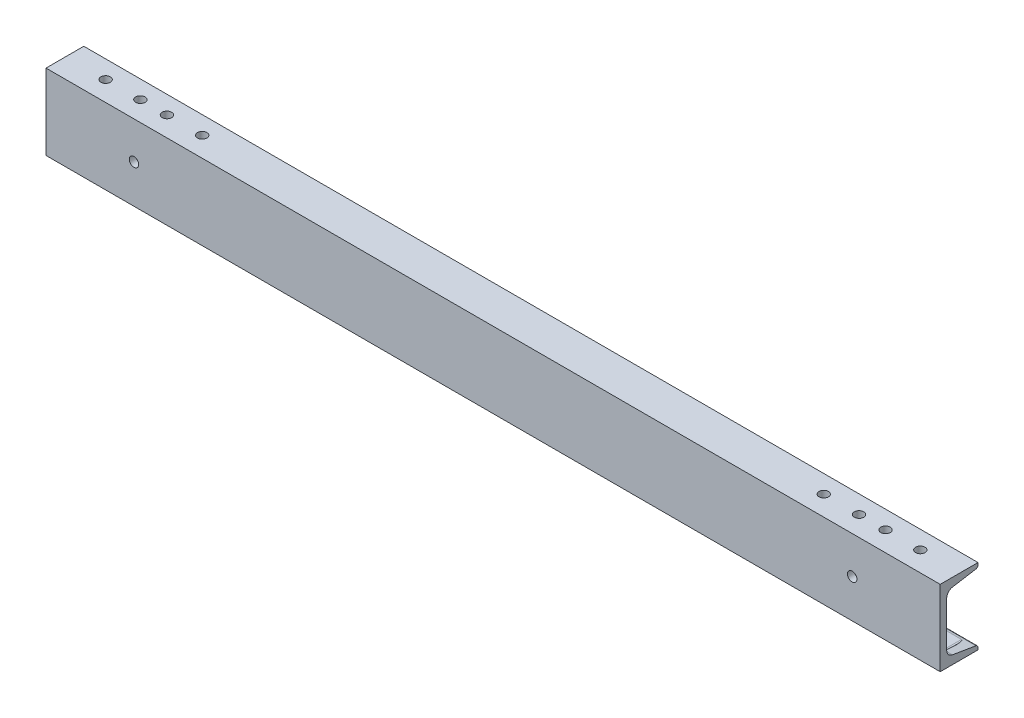
SolidWorks part; units mm, degrees
material "Plain Carbon Steel"
ref_plane "Front Plane" through (0, 0, 0) normal (0, 0, 1) x (1, 0, 0)
ref_plane "Top Plane" through (0, 0, 0) normal (0, 1, 0) x (1, 0, 0)
ref_plane "Right Plane" through (0, 0, 0) normal (1, 0, 0) x (0, 0, -1)
sketch "Sketch1" plane through (0, 0, 0) normal (0, 1, 0) x (1, 0, 0)
  line L0 (-450, 0) -> (450, 0)
  dimension "D1" = 900
other "Structural Member1"
ref_plane "Plane1" through (-450, 0, 0) normal (1, 0, 0) x (0, 0, -1)
sketch "Sketch11" plane through (-450, 0, 0) normal (1, 0, 0) x (0, 0, -1)
  line L0 (0, -38.1) -> (0, 38.1)
  line L1 (0, 38.1) -> (38.0492, 38.1)
  line L2 (0, -38.1) -> (38.0492, -38.1)
  line L5 (31.75, -31.1658) -> (6.35, -31.1658) construction
  line L6 (0, 0) -> (6.5532, 0) construction
  line L12 (6.5532, 22.7314) -> (6.5532, -22.7314)
  line L15 (38.0492, 38.1) -> (38.0492, 35.9423)
  line L16 (38.0492, -38.1) -> (38.0492, -35.9423)
  line L17 (12.2837, 29.4961) -> (35.9268, 33.4369)
  line L18 (12.2837, -29.4961) -> (35.9268, -33.4369)
  arc A9 (6.5532, -22.7314) -> (12.2837, -29.4961) centre (13.4112, -22.7314) ccw
  arc A10 (6.5532, 22.7314) -> (12.2837, 29.4961) centre (13.4112, 22.7314) cw
  arc A11 (38.0492, 35.9423) -> (35.9268, 33.4369) centre (35.5092, 35.9423) cw
  arc A12 (38.0492, -35.9423) -> (35.9268, -33.4369) centre (35.5092, -35.9423) ccw
  point P4 (38.0492, 33.7907)
  point P5 (38.0492, -33.7907)
  point P6 (3.2766, 0)
  point P7 (19.0246, 38.1)
  point P12 (19.0246, -38.1)
  point P13 (0, 0)
  dimension "RI" = 6.858
  dimension "D2" = 9.463
  dimension "RA" = 2.54
  dimension "Depth" = 76.2
  dimension "BF" = 38.0492
  dimension "TW" = 6.5532
  dimension "flange" = 2.1577
  dimension "TF" = 6.9342
sketch "Sketch12" plane through (0, 0, 0) normal (0, 1, 0) x (1, 0, 0)
  line L0 (-412.5239, 20) -> (413.742, 20) construction
  line L1 (-450, 0) -> (450, 0) construction
  line L2 (0, 0) -> (0, 45.9021) construction
  line L3 (-450, 38.0492) -> (-450, 0) construction
  circle A0 centre (-425, 20) radius 4.7625
  circle A1 centre (425, 20) radius 4.7625
  dimension "D2" = 9.525
  dimension "D1" = 20
  dimension "D3" = 25
extrude "Cut-Extrude1" cut sketch "Sketch12" against normal through all
sketch "Sketch15" plane through (0, 0, -6.5532) normal (0, 0, -1) x (-1, 0, 0)
  line L0 (-425, -21.1359) -> (-425, -40.4286) construction
  line L1 (-375.1366, -28.1) -> (-474.8634, -28.1) construction
  line L2 (-450, -38.1) -> (450, -38.1) construction
  line L3 (-412.5, -28.1) -> (-437.5, -28.1) construction
  line L4 (-412.5, -33.1) -> (-437.5, -33.1)
  line L5 (-412.5, -23.1) -> (-437.5, -23.1)
  line L6 (0, 0) -> (0, -58.1771) construction
  line L7 (412.5, -28.1) -> (437.5, -28.1) construction
  line L8 (412.5, -33.1) -> (437.5, -33.1)
  line L9 (412.5, -23.1) -> (437.5, -23.1)
  arc A0 (-412.5, -33.1) -> (-412.5, -23.1) centre (-412.5, -28.1) ccw
  arc A1 (-437.5, -23.1) -> (-437.5, -33.1) centre (-437.5, -28.1) ccw
  arc A2 (412.5, -33.1) -> (412.5, -23.1) centre (412.5, -28.1) cw
  arc A3 (437.5, -23.1) -> (437.5, -33.1) centre (437.5, -28.1) cw
  ellipse E0 centre (-425, -30.7822) end of major axis (-429.7625, -30.7822) minor radius 0.7938 construction
  point P0 (-425, -30.7822)
  point P11 (-425, -28.1)
  point P16 (-425, -28.1)
  point P26 (425, -28.1)
  dimension "D2" = 5
  dimension "D1" = 10
  dimension "D3" = 25
extrude "Cut-Extrude2" cut sketch "Sketch15" along normal blind 40
sketch "Sketch16" plane through (0, 0, 0) normal (0, 1, 0) x (1, 0, 0)
  line L0 (0, -46.4014) -> (0, 86.4014) construction
  line L1 (-444.6056, 20) -> (444.6056, 20) construction
  line L2 (450, 0) -> (-450, 0) construction
  circle A0 centre (-348.3, 20) radius 4.7625
  circle A1 centre (-312.8, 20) radius 4.7625
  circle A2 centre (312.8, 20) radius 4.7625
  circle A3 centre (348.3, 20) radius 4.7625
  circle A4 centre (-375, 20) radius 4.7625
  circle A5 centre (-410, 20) radius 4.7625
  circle A6 centre (375, 20) radius 4.7625
  circle A7 centre (410, 20) radius 4.7625
  point P5 (0, 20)
  point P6 (0, 20)
  dimension "D2" = 9.525
  dimension "D1" = 20
  dimension "D3" = 348.3
  dimension "D4" = 35.5
  dimension "D5" = 35
  dimension "D6" = 410
extrude "Cut-Extrude3" cut sketch "Sketch16" along normal through all
sketch "Sketch17" plane through (0, 0, 0) normal (0, 0, 1) x (1, 0, 0)
  circle A0 centre (-361.4375, 0.6) radius 4.7625 construction
  circle A1 centre (361.4375, 0.6) radius 4.7625 construction
  circle A2 centre (-361.4375, 0.6) radius 4.7625
  circle A3 centre (361.4375, 0.6) radius 4.7625
extrude "Cut-Extrude4" cut sketch "Sketch17" against normal through all
